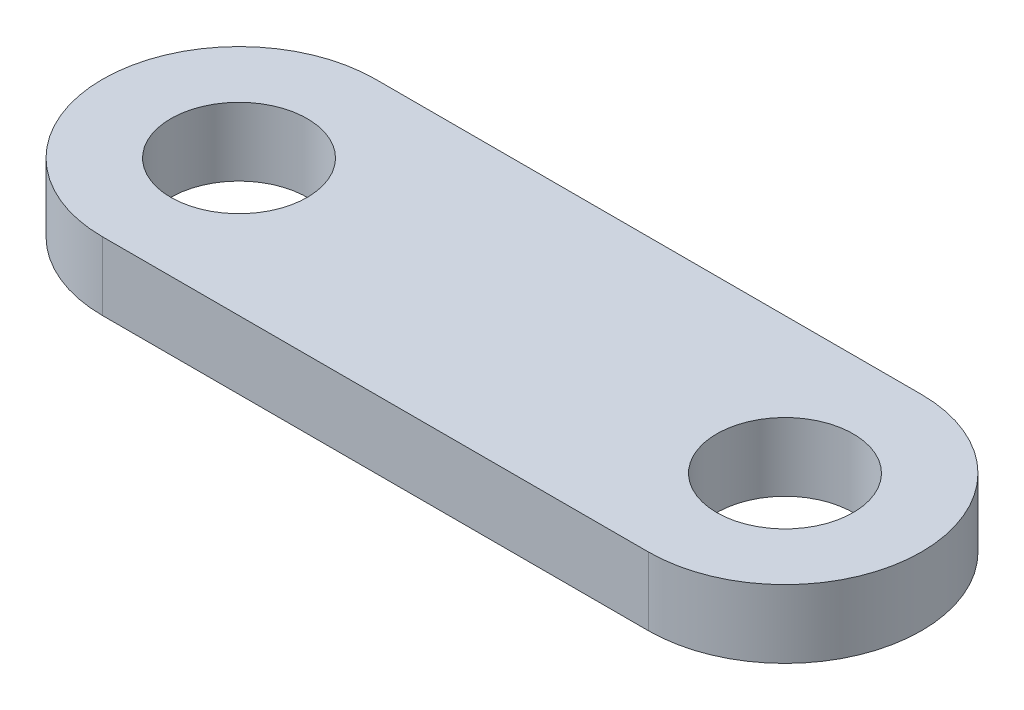
SolidWorks part; units mm, degrees
ref_plane "Front Plane" through (0, 0, 0) normal (0, 0, 1) x (1, 0, 0)
ref_plane "Top Plane" through (0, 0, 0) normal (0, 1, 0) x (1, 0, 0)
ref_plane "Right Plane" through (0, 0, 0) normal (1, 0, 0) x (0, 0, -1)
sketch "Sketch3" plane through (0, 0, 0) normal (0, 1, 0) x (1, 0, 0)
  line L0 (-20, 0) -> (20, 0) construction
  line L1 (-20, 10) -> (20, 10)
  line L2 (-20, -10) -> (20, -10)
  arc A0 (-20, 10) -> (-20, -10) centre (-20, 0) ccw
  arc A1 (20, -10) -> (20, 10) centre (20, 0) ccw
  circle A2 centre (-20, 0) radius 5
  circle A3 centre (20, 0) radius 5
  point P2 (0, 0)
  dimension "D3" = 10
  dimension "D4" = 10
  dimension "D1" = 40
  dimension "D2" = 20
extrude "Boss-Extrude1" add sketch "Sketch3" along normal blind 5
